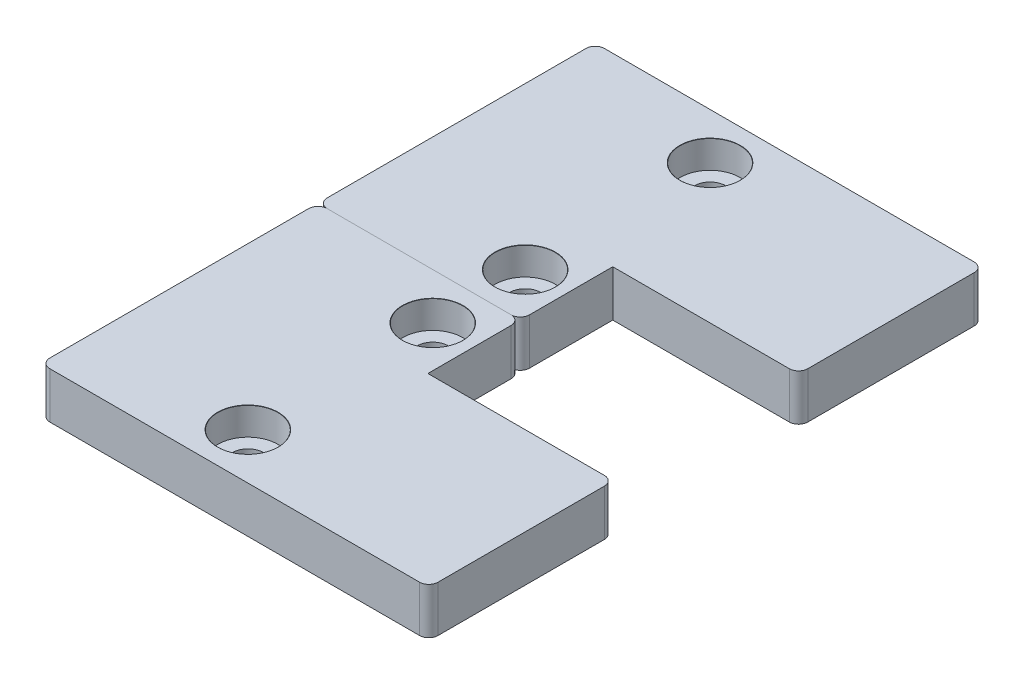
SolidWorks part; units mm, degrees
ref_plane "Front Plane" through (0, 0, 0) normal (0, 0, 1) x (1, 0, 0)
ref_plane "Top Plane" through (0, 0, 0) normal (0, 1, 0) x (1, 0, 0)
ref_plane "Right Plane" through (0, 0, 0) normal (1, 0, 0) x (0, 0, -1)
sketch "Sketch1" plane through (0, 0, 0) normal (0, 1, 0) x (1, 0, 0)
  line L1 (21, 10) -> (-21, 10)
  line L2 (21, 10) -> (21, -10)
  line L3 (21, -10) -> (-21, -10)
  line L4 (-21, 10) -> (-21, -10)
  line L5 (21, 10) -> (-21, -10) construction
  line L6 (21, -10) -> (-21, 10) construction
  point P0 (0, 0)
  dimension "D1" = 42
  dimension "D2" = 20
extrude "Boss-Extrude1" add sketch "Sketch1" along normal blind 5
sketch "Sketch2" plane through (0, 5, 0) normal (0, 1, 0) x (1, 0, 0)
  line L0 (21, -10) -> (21, 10) construction
  line L1 (-21, 10) -> (0.9, 10)
  line L2 (-21, 10) -> (-21, 20)
  line L3 (-21, 20) -> (0.9, 20)
  line L4 (0.9, 10) -> (0.9, 20)
  dimension "D1" = 20.1
  dimension "D2" = 10
extrude "Boss-Extrude2" add sketch "Sketch2" against normal blind 5
sketch "Sketch3" plane through (0, 5, 0) normal (0, 1, 0) x (1, 0, 0)
  line L0 (-21, 5) -> (21, 5) construction
  line L1 (-21, 20) -> (-21, -10) construction
  line L2 (21, -10) -> (21, 10) construction
  line L3 (-3.575, 20) -> (-3.575, -10) construction
  line L4 (0.9, 20) -> (-21, 20) construction
  line L5 (-21, -10) -> (21, -10) construction
  line L6 (0.9, 10) -> (0.9, 20) construction
  line L7 (-3.575, 15) -> (-3.575, -5) construction
  point P17 (-3.575, 5)
  dimension "D1" = 4.475
  dimension "D2" = 20
hole_wizard "CBORE for M3 SHCS1" positions "Sketch6" profile "Sketch7" counterbore size "M3" standard "ANSI Metric" end condition through all
sketch "Sketch6" plane through (0, 5, 0) normal (0, 1, 0) x (1, 0, 0)
  point P0 (-3.575, 15)
  point P3 (-3.575, -5)
sketch "Sketch7" plane through (-3.575, 5, -15) normal (1, 0, 0) x (0, 0, 1)
  line L0 (0, 0) -> (0, 5)
  line L1 (0, 5) -> (1.7, 5)
  line L3 (1.7, 5) -> (1.7, 3)
  line L4 (3.25, 3) -> (1.7, 3)
  line L5 (3.25, 3) -> (3.25, 0.021)
  line L6 (3.25, 0.021) -> (3.275, 0)
  line L7 (3.275, 0) -> (0, 0)
  line L8 (-3.25, 0.021) -> (-3.275, 0) construction
  line L11 (0, -6.35) -> (0, 107.95) construction
  dimension "Thru Hole Dia." = 3.4
  dimension "Thru Hole Depth" = 5
  dimension "C'Bore Dia." = 6.5
  dimension "C'Bore Depth" = 3
  dimension "Near C'Sink Dia." = 6.55
  dimension "Near C'Sink Angle" = 100
fillet "Fillet1" radius 1 5 edges at (-21, 2.5, -20) (0.9, 2.5, -20) (21, 2.5, -10) (21, 2.5, 10) (-21, 2.5, 10)
mirror "Mirror1" about plane through (-21, 0, -20) normal (0, 0, -1) of bodies 103
